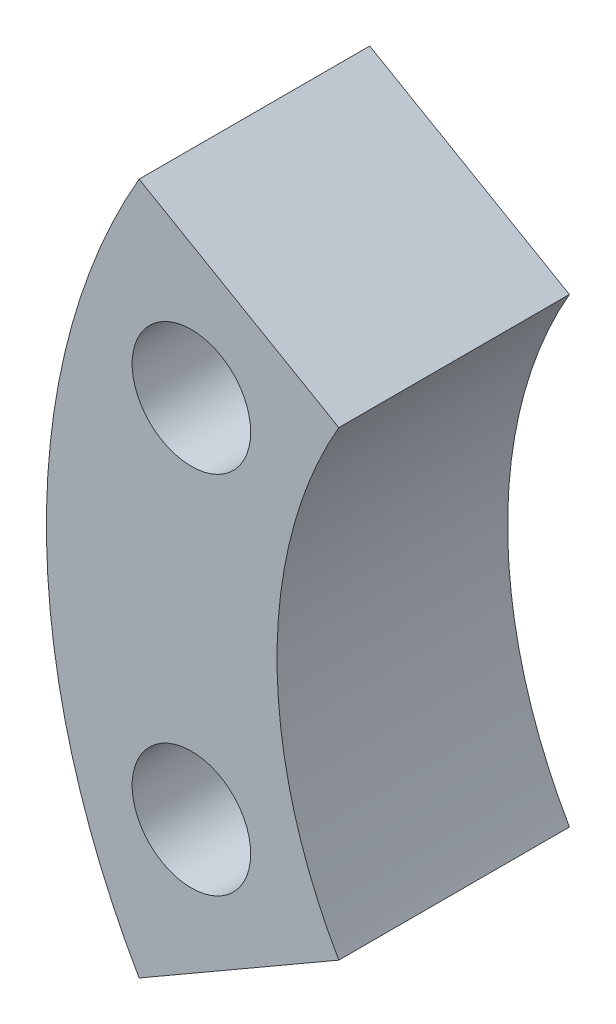
SolidWorks part; units mm, degrees
ref_plane "Front Plane" through (0, 0, 0) normal (1, 0, 0) x (0, 1, 0)
ref_plane "Top Plane" through (0, 0, 0) normal (0, 0, 1) x (0, 1, 0)
ref_plane "Right Plane" through (0, 0, 0) normal (0, 1, 0) x (-1, 0, 0)
sketch "Sketch1" plane through (0, 0, 0) normal (0, 0, 1) x (0, 1, 0)
  line L0 (0, 0) -> (9.525, 16.4978) construction
  line L1 (9.525, 16.4978) -> (-9.525, 16.4978) construction
  line L2 (-9.525, 16.4978) -> (0, 0) construction
  line L3 (-9.525, 16.4978) -> (-6.35, 10.9985)
  line L4 (9.525, 16.4978) -> (6.35, 10.9985)
  arc A0 (6.35, 10.9985) -> (-6.35, 10.9985) centre (0, 0) ccw
  arc A1 (9.525, 16.4978) -> (-9.525, 16.4978) centre (0, 0) ccw
  dimension "D1" = 25.4
  dimension "D2" = 38.1
  dimension "D3" = 19.05
extrude "Boss-Extrude1" add sketch "Sketch1" along normal blind 6.35
sketch "Sketch2" plane through (0, 0, 6.35) normal (0, 0, 1) x (1, 0, 0)
  line L0 (-10.9985, 6.35) -> (-16.4978, 9.525) construction
  line L1 (-16.4978, -9.525) -> (-10.9985, -6.35) construction
  line L2 (-15.0579, 5.0275) -> (0, 0) construction
  line L3 (0, 0) -> (-15.0579, -5.0275) construction
  circle A1 centre (-15.0579, 5.0275) radius 1.632
  circle A2 centre (-15.0579, -5.0275) radius 1.632
  point P3 (-15.0579, 5.0275)
  point P4 (-15.0579, -5.0275)
  dimension "D1" = 15.875
  dimension "D5" = 3.2639
  dimension "D6" = 3.2639
  dimension "D2" = 3.175
  dimension "D3" = 3.175
  dimension "D4" = 15.875
extrude "Cut-Extrude1" cut sketch "Sketch2" against normal up to next
